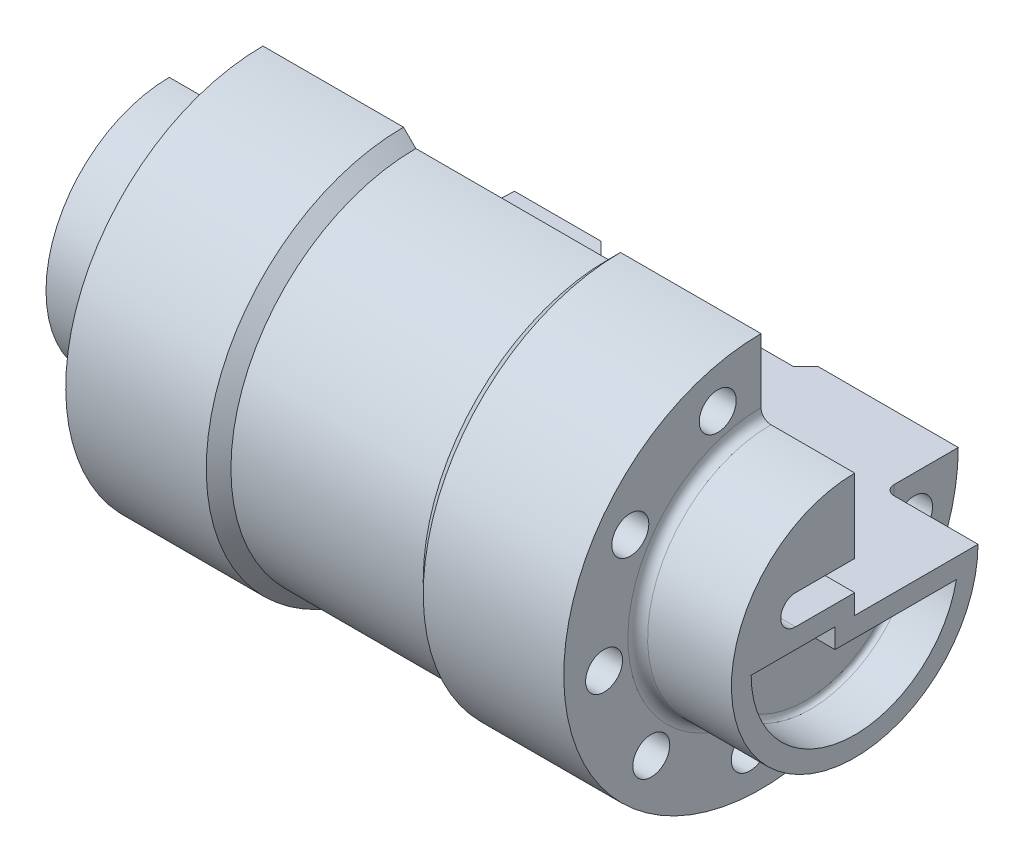
SolidWorks part; units mm, degrees
material "AISI 1020"
ref_plane "Front Plane" through (0, 0, 0) normal (0, 0, 1) x (1, 0, 0)
ref_plane "Top Plane" through (0, 0, 0) normal (0, 1, 0) x (1, 0, 0)
ref_plane "Right Plane" through (0, 0, 0) normal (1, 0, 0) x (0, 0, -1)
sketch "Sketch1" plane through (0, 0, 0) normal (0, 1, 0) x (1, 0, 0)
  line L0 (0, 0) -> (0, 25)
  line L1 (0, 25) -> (17, 25)
  line L2 (19, 27) -> (19, 40)
  line L3 (19, 40) -> (47.5, 40)
  line L4 (47.5, 40) -> (50, 37.5)
  line L5 (50, 37.5) -> (89, 37.5)
  line L6 (89, 37.5) -> (91.5, 40)
  line L7 (91.5, 40) -> (120, 40)
  line L8 (120, 40) -> (120, 27)
  line L9 (122, 25) -> (139, 25)
  line L10 (139, 25) -> (139, 0)
  line L11 (139, 0) -> (0, 0) construction
  line L12 (0, 0) -> (139, 0)
  arc A0 (120, 27) -> (122, 25) centre (122, 27) ccw
  arc A1 (17, 25) -> (19, 27) centre (17, 27) ccw
  point P15 (120, 25)
  point P18 (19, 25)
  dimension "D13" = 2
  dimension "D1" = 40
  dimension "D2" = 25
  dimension "D3" = 40
  dimension "D4" = 25
  dimension "D5" = 139
  dimension "D6" = 19
  dimension "D7" = 19
  dimension "D8" = 28.5
  dimension "D9" = 28.5
  dimension "D10" = 2.5
  dimension "D11" = 45
  dimension "D12" = 45
revolve "Revolve2" add sketch "Sketch1" angle 270 about L11
sketch "Sketch2" plane through (139, 0, 0) normal (1, 0, 0) x (0, 0, -1)
  line L0 (0, 0) -> (0, 25) construction
  line L1 (0, 0) -> (25, 0) construction
  line L3 (-12, 4) -> (0, 4)
  line L5 (-12, 10) -> (0, 10)
  line L6 (0, 4) -> (0, 10)
  arc A0 (-12, 10) -> (-12, 4) centre (-12, 7) ccw
  dimension "D1" = 6
  dimension "D2" = 12
  dimension "D3" = 7
  dimension "D4" = 12
extrude "Cut-Extrude1" cut sketch "Sketch2" against normal up to next
sketch "Sketch3" plane through (120, 0, 0) normal (1, 0, 0) x (0, 0, -1)
  circle A3 centre (-8.7832, 30.771) radius 3.75
  circle A6 centre (31.0401, -7.779) radius 3.75
  circle A7 centre (18.7778, -25.9113) radius 3.75
  circle A8 centre (-2.2708, -31.9193) radius 3.75
  circle A9 centre (-22.2569, -22.992) radius 3.75
  circle A10 centre (-31.8287, -3.3064) radius 3.75
  circle A11 centre (-26.5075, 17.9262) radius 3.75
  arc A12 (9.5432, 30.5438) -> (16.3794, 27.4903) centre (13.0509, 29.2177) ccw
  arc A13 (30.2177, 10.5303) -> (26.9437, 17.2637) centre (28.7784, 13.9931) ccw
  point P24 (0, 0)
  dimension "D3" = 7.5
  dimension "D2" = 9
extrude "Cut-Extrude2" cut sketch "Sketch3" against normal up to next
sketch "Sketch4" plane through (0, 0, 0) normal (0, 1, 0) x (1, 0, 0)
  line L0 (19, 40) -> (0, 40) construction
  line L1 (0, 40) -> (0, 25) construction
  line L2 (0, 40) -> (0, 10)
  line L3 (0, 40) -> (30, 40)
  line L4 (6.0777, 5.5317) -> (5.2094, 10.4558)
  line L5 (33.5262, 29.9505) -> (28.9384, 32.0899)
  arc A0 (6.0777, 5.5317) -> (33.5262, 29.9505) centre (0, 40) ccw
  arc A1 (0, 10) -> (5.2094, 10.4558) centre (0, 40) ccw
  arc A2 (28.9384, 32.0899) -> (30, 40) centre (0, 40) ccw
  dimension "D1" = 70
  dimension "D2" = 60
  dimension "D4" = 25
  dimension "D3" = 10
  dimension "D5" = 4.5878
extrude "Cut-Extrude3" cut sketch "Sketch4" against normal through all
sketch "Sketch5" plane through (139, 0, 0) normal (1, 0, 0) x (0, 0, -1)
  line L2 (25, 0) -> (21, 0)
  line L5 (-4, 0) -> (-12, 0)
  line L6 (20.6155, -4) -> (0, -4)
  line L7 (-12, 0) -> (-21, 0)
  line L8 (25, 0) -> (0, 0) construction
  line L9 (-4, 0) -> (-4, -4)
  line L10 (-4, -4) -> (0, -4)
  line L11 (25, -4) -> (0, -4) construction
  arc A1 (-21, 0) -> (20.6155, -4) centre (0, 0) ccw
  dimension "D3" = 4
extrude "Cut-Extrude4" cut sketch "Sketch5" against normal blind 10 contours A1 L6 L10 L9 L5 L7
fillet "Fillet1" radius 1 4 edges at (129, -2, 4) (129, -4, -8.3078) (129, -20.9037, 2.0092) (129, 0, 12.5)
equation "\"A\"= 139"
equation "\"B\"= 19"
equation "\"C\"= 28.50"
